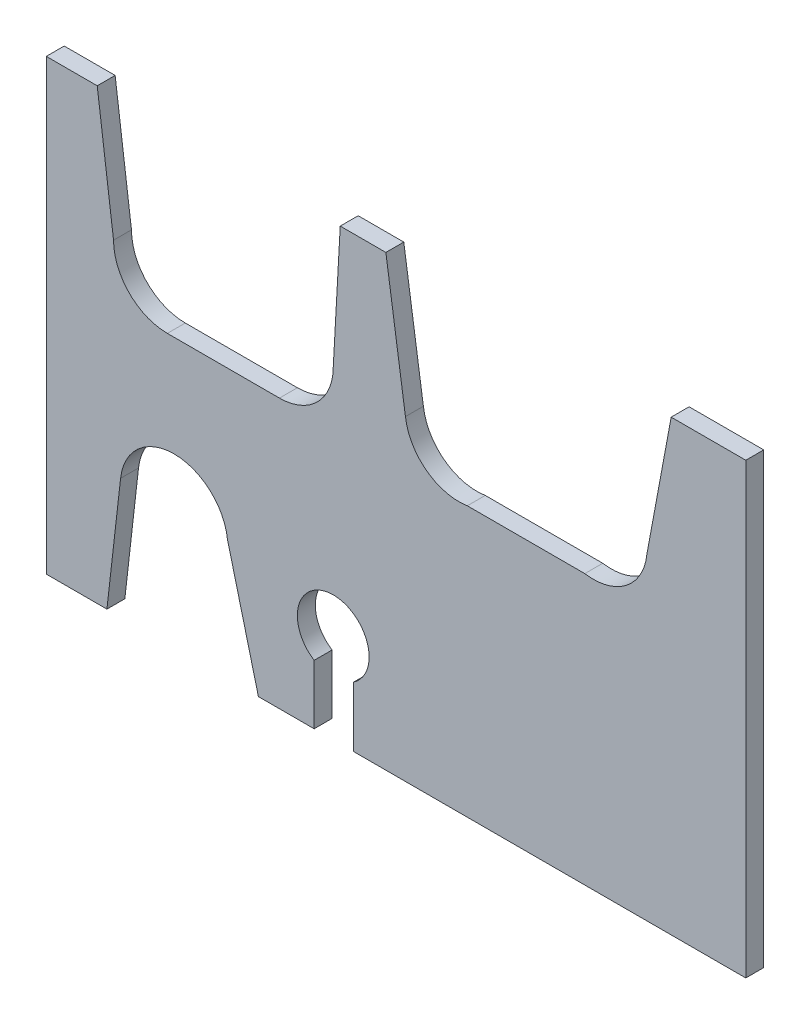
SolidWorks part; units mm, degrees
ref_plane "Спереди" through (0, 0, 0) normal (0, 0, 1) x (1, 0, 0)
ref_plane "Сверху" through (0, 0, 0) normal (0, 1, 0) x (1, 0, 0)
ref_plane "Справа" through (0, 0, 0) normal (1, 0, 0) x (0, 0, -1)
sketch "Эскиз1" plane through (0, 0, 0) normal (0, 0, 1) x (1, 0, 0)
  line L1 (-46, 32) -> (32, 32)
  line L2 (-46, 32) -> (-46, -18)
  line L3 (-46, -18) -> (32, -18)
  line L4 (32, 32) -> (32, -18)
  point P0 (0, 0)
  point P6 (-71.0413, -32.1586)
  point P7 (55.0205, 37.8887)
  point P8 (-58.9964, 32.9772)
  point P9 (0, 0)
  point P10 (0, 0)
  point P11 (0, 0)
  point P12 (0, 0)
  point P13 (0, 0)
  dimension "D1" = 50
  dimension "D2" = 78
extrude "Бобышка-Вытянуть1" add sketch "Эскиз1" along normal blind 2
sketch "Эскиз2" plane through (0, 0, 2) normal (0, 0, 1) x (1, 0, 0)
  circle A0 centre (-32.5, 18) radius 6
  circle A1 centre (-20, 18) radius 6
  circle A2 centre (0, 18) radius 6
  circle A3 centre (15, 18) radius 6
  circle A4 centre (-14, -8) radius 4
  circle A5 centre (-31.7493, -5.2623) radius 6
  point P12 (-31.7493, -5.2623)
  point P13 (-14.3098, -8.0926)
extrude "Вырез-Вытянуть2" cut sketch "Эскиз2" against normal through all
sketch "Эскиз3" plane through (0, 0, 2) normal (0, 0, 1) x (1, 0, 0)
  line L0 (-37.7087, -4.5657) -> (-39.2383, -18)
  line L1 (-46, -18) -> (32, -18) construction
  line L2 (-39.2383, -18) -> (-22.3456, -18)
  line L3 (-22.3456, -18) -> (-25.7899, -4.5657)
  line L4 (-25.7899, -4.5657) -> (-37.7087, -4.5657)
  line L5 (-16.1286, -11.3866) -> (-16.1286, -18)
  line L6 (-16.1286, -18) -> (-11.7335, -18)
  line L7 (-11.7335, -18) -> (-11.7335, -11.2959)
  line L8 (-11.7335, -11.2959) -> (-16.1286, -11.3866)
  line L9 (-40.3196, 32) -> (-38.5, 18)
  line L10 (32, 32) -> (-46, 32) construction
  line L11 (-38.5, 18) -> (-32.5, 12)
  line L12 (-32.5, 12) -> (-20, 12)
  line L13 (-20, 12) -> (-14, 18)
  line L14 (-14, 18) -> (-13.2215, 32)
  line L15 (-13.2215, 32) -> (-40.3196, 32)
  line L16 (-8.1344, 32) -> (-5.9174, 17.0078)
  line L17 (-5.9174, 17.0078) -> (-0.9491, 12.0755)
  line L18 (-0.9491, 12.0755) -> (15.9491, 12.0755)
  line L19 (15.9491, 12.0755) -> (20.785, 16.4081)
  line L20 (20.785, 16.4081) -> (23.68, 32)
  line L21 (23.68, 32) -> (-8.1344, 32)
  circle A0 centre (-31.7493, -5.2623) radius 6 construction
  circle A1 centre (-14, -8) radius 4 construction
  circle A2 centre (-32.5, 18) radius 6 construction
  circle A3 centre (-20, 18) radius 6 construction
  circle A4 centre (0, 18) radius 6 construction
  circle A5 centre (15, 18) radius 6 construction
  point P30 (-16.1286, -32.1586)
  point P37 (-5.9174, 17.0078)
  point P38 (-14.016, 17.5622)
  point P39 (-38.285, 16.4081)
  point P40 (-20, 12)
  point P41 (-14, 18)
  point P42 (-37.7493, -5.2623)
  point P43 (-25.9265, -18)
  point P44 (-25.9265, -18)
  point P45 (-22.9909, -18)
  point P46 (-25.7493, -5.2623)
  point P47 (-39.4093, -18)
  point P48 (-25.7493, -5.2623)
  point P49 (-40.3196, -18)
  point P50 (-25.7493, -5.2623)
  point P51 (-39.2383, -18)
extrude "Вырез-Вытянуть3" cut sketch "Эскиз3" against normal through all
